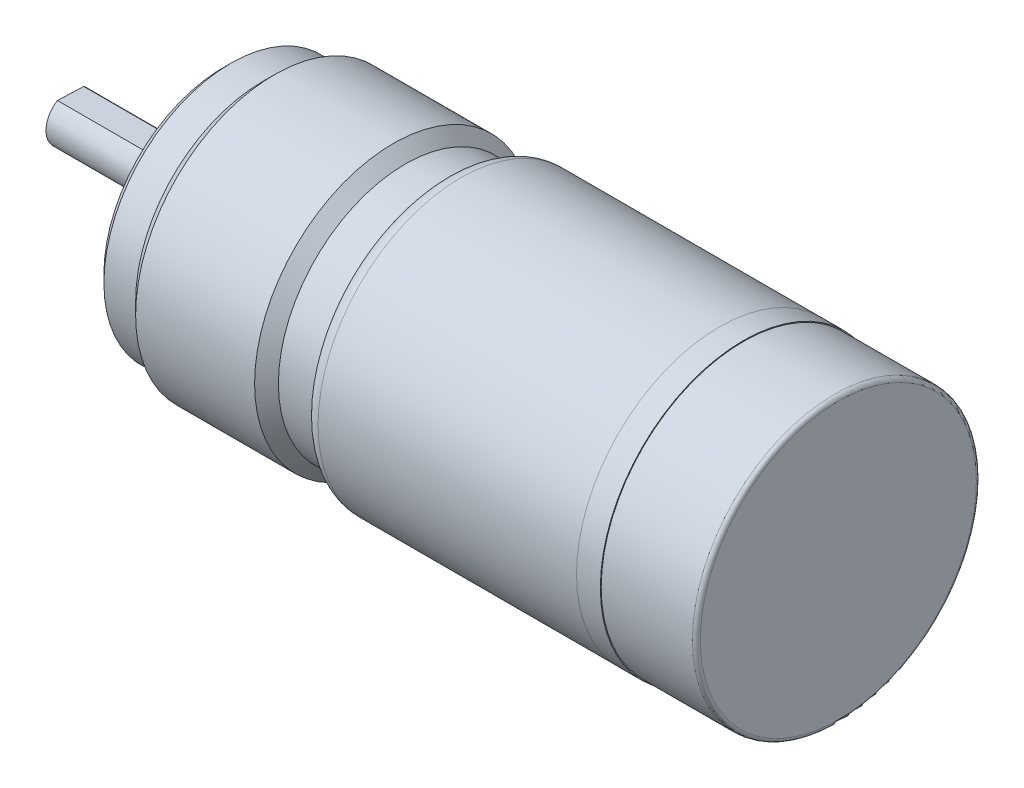
SolidWorks part; units mm, degrees
ref_plane "Спереди" through (0, 0, 0) normal (0, 0, 1) x (1, 0, 0)
ref_plane "Сверху" through (0, 0, 0) normal (0, 1, 0) x (1, 0, 0)
ref_plane "Справа" through (0, 0, 0) normal (1, 0, 0) x (0, 0, -1)
sketch "Эскиз1" plane through (0, 0, 0) normal (0, 1, 0) x (1, 0, 0)
  line L0 (0, 0) -> (104.9, 0) construction
  line L1 (24.3, 16) -> (25.8, 17.5)
  line L2 (0, 0) -> (16.3, 0)
  line L3 (0, 0) -> (0, 3)
  line L4 (0, 3) -> (16.3, 3)
  line L5 (16.3, 0) -> (16.3, 3)
  line L6 (16.3, 0) -> (19.3, 0)
  line L7 (16.3, 0) -> (16.3, 10)
  line L8 (16.3, 10) -> (19.3, 10)
  line L9 (19.3, 0) -> (19.3, 10)
  line L10 (19.3, 0) -> (24.3, 0)
  line L11 (19.3, 0) -> (19.3, 15)
  line L12 (20.3, 16) -> (24.3, 16)
  line L13 (24.3, 0) -> (24.3, 16)
  line L14 (24.3, 0) -> (42.3, 0)
  line L15 (24.3, 0) -> (24.3, 16)
  line L16 (25.8, 17.5) -> (40.8, 17.5)
  line L17 (42.3, 0) -> (42.3, 16)
  line L18 (19.3, 15) -> (20.3, 16)
  line L19 (40.8, 17.5) -> (42.3, 16)
  line L21 (42.3, 0) -> (47.3, 0)
  line L22 (42.3, 0) -> (42.3, 16)
  line L23 (42.3, 16) -> (47.3, 16)
  line L24 (47.3, 0) -> (47.3, 16)
  line L25 (47.3, 0) -> (86.4, 0)
  line L26 (47.3, 0) -> (47.3, 16)
  line L27 (49.3, 18) -> (86.4, 18)
  line L28 (86.4, 0) -> (86.4, 18)
  arc A0 (47.3, 16) -> (49.3, 18) centre (49.3, 16) cw
  point P10 (19.3, 16)
  point P12 (42.3, 17.5)
  point P13 (24.3, 17.5)
  point P28 (47.3, 18)
  dimension "D14" = 2
  dimension "D1" = 104.9
  dimension "D2" = 3
  dimension "D3" = 16.3
  dimension "D4" = 3
  dimension "D5" = 10
  dimension "D6" = 16
  dimension "D7" = 5
  dimension "D8" = 17.5
  dimension "D9" = 18
  dimension "D10" = 5
  dimension "D11" = 18
  dimension "D12" = 39.1
revolve "Повернуть1" add sketch "Эскиз1" angle 360 about L0
sketch "Эскиз4" plane through (86.4, 0, 0) normal (1, 0, 0) x (0, 0, -1)
  circle A0 centre (0, 0) radius 18
extrude "Бобышка-Вытянуть1" add sketch "Эскиз4" along normal blind 14
sketch "Эскиз5" plane through (100.4, 0, 0) normal (1, 0, 0) x (0, 0, -1)
  circle A0 centre (0, 0) radius 18
extrude "Вырез-Вытянуть2" cut sketch "Эскиз5" against normal blind 3.5
sketch "Эскиз6" plane through (0, 0, 0) normal (-1, 0, 0) x (0, 0, 1)
  line L0 (1.5611, 2.5618) -> (-1.7531, 2.4345)
  circle A0 centre (0, 0) radius 3
  circle M1 centre (0, 0) radius 3
  dimension "D2" = 6
  dimension "D1" = 2.5
extrude "Вырез-Вытянуть4" cut sketch "Эскиз6" against normal blind 12 contours L0 M1
sketch "Эскиз8" plane through (0, 0, 0) normal (0, 1, 0) x (1, 0, 0)
  line L0 (96.9, 0) -> (98.9645, 0) construction
  line L1 (96.9, -18) -> (84.9, -18)
  line L2 (96.9, -18) -> (96.9, -17.9)
  line L3 (96.9, -17.9) -> (84.9, -17.9)
  line L4 (84.9, -18) -> (84.9, -17.9)
  line L5 (96.9, -18) -> (96.9, 18) construction
  dimension "D1" = 0.1
  dimension "D2" = 12
sketch "Эскиз9" plane through (96.9, 0, 0) normal (1, 0, 0) x (0, 0, -1)
  circle A0 centre (0, 0) radius 17.9
  dimension "D1" = 35.8
sweep "Вырез-По траектории3" cut profiles "Эскиз8" path "Эскиз9"
fillet "Скругление3" radius 0.5 1 edges at (96.9, 0, 17.9)
sketch "Эскиз10" plane through (0, 0, 0) normal (0, 1, 0) x (1, 0, 0)
  line L0 (0, 0) -> (119.0567, 0) construction
  line L1 (84.9, 18) -> (81.9, 18)
  line L2 (84.9, 18) -> (84.9, 18.01)
  line L3 (84.9, 18.01) -> (81.9, 18.01)
  line L4 (81.9, 18) -> (81.9, 18.01)
  dimension "D1" = 0.01
  dimension "D2" = 3
revolve "Повернуть2" add sketch "Эскиз10" angle 360 about L0
sketch "Эскиз11" plane through (16.3, 0, 0) normal (-1, 0, 0) x (0, 0, 1)
  line L0 (-4.3589, 9) -> (4.3589, 9)
  line L1 (4.3589, -9) -> (-4.3589, -9)
  circle A0 centre (0, 0) radius 10 construction
  circle A3 centre (0, 0) radius 10
  circle M1 centre (0, 0) radius 10
  dimension "D1" = 18
  dimension "D2" = 9
extrude "Вырез-Вытянуть6" cut sketch "Эскиз11" against normal blind 3 contours L0 M1 | L1 M1
sketch "Эскиз13" plane through (19.3, 0, 0) normal (-1, 0, 0) x (0, 0, 1)
  line L0 (0, 0) -> (-9.1924, 9.1924)
  circle A0 centre (0, 0) radius 13
  circle A2 centre (-9.1924, 9.1924) radius 1.5
  dimension "D1" = 26
  dimension "D2" = 3
extrude "Вырез-Вытянуть8" cut sketch "Эскиз13" against normal blind 7 contours A0 A2 | L0 A2 A0 | A0 A2 L0
pattern_circular "Круговой массив2" count 4 every 90 about axis through (0, 0, 0) along (1, 0, 0) of "Вырез-Вытянуть8"
